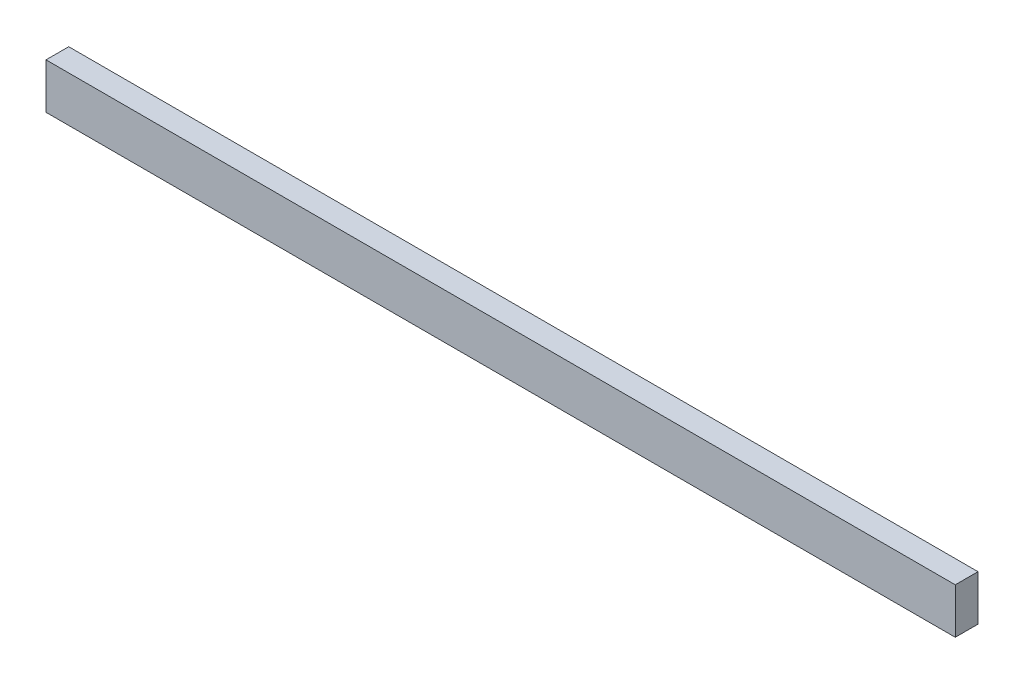
SolidWorks part; units mm, degrees
ref_plane "Front Plane" through (0, 0, 0) normal (0, 0, 1) x (1, 0, 0)
ref_plane "Top Plane" through (0, 0, 0) normal (0, 1, 0) x (1, 0, 0)
ref_plane "Right Plane" through (0, 0, 0) normal (1, 0, 0) x (0, 0, -1)
sketch "Sketch1" plane through (0, 0, 0) normal (0, 0, 1) x (1, 0, 0)
  line L1 (-127, -6.35) -> (127, -6.35)
  line L2 (-127, -6.35) -> (-127, 6.35)
  line L3 (-127, 6.35) -> (127, 6.35)
  line L4 (127, -6.35) -> (127, 6.35)
  line L5 (-127, -6.35) -> (127, 6.35) construction
  line L6 (-127, 6.35) -> (127, -6.35) construction
  point P0 (0, 0)
  dimension "D1" = 12.7
  dimension "D2" = 254
extrude "Boss-Extrude1" add sketch "Sketch1" along normal blind 6.35
